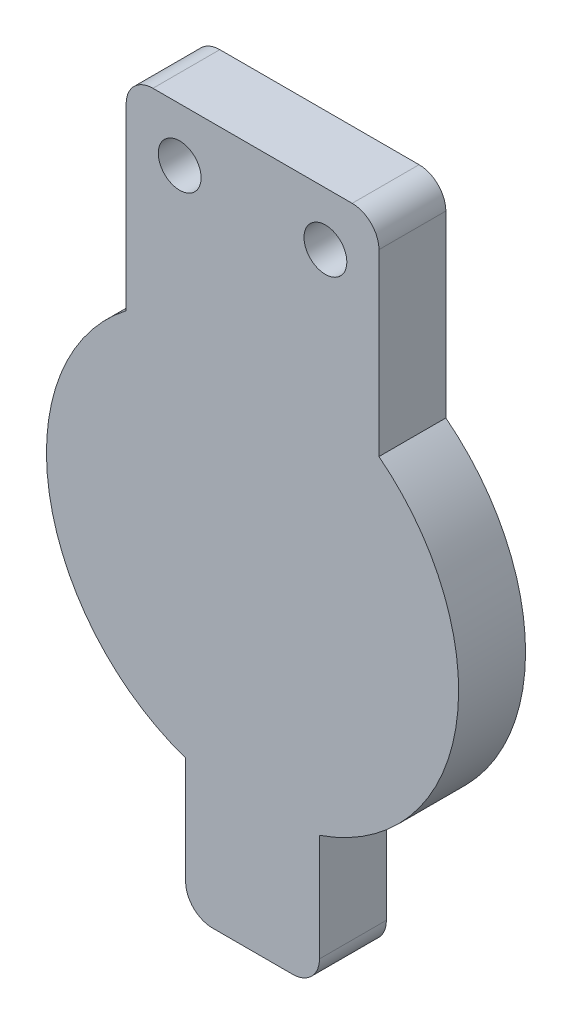
SolidWorks part; units mm, degrees
ref_plane "Front Plane" through (0, 0, 0) normal (0, 0, 1) x (1, 0, 0)
ref_plane "Top Plane" through (0, 0, 0) normal (0, 1, 0) x (1, 0, 0)
ref_plane "Right Plane" through (0, 0, 0) normal (1, 0, 0) x (0, 0, -1)
sketch "Sketch1" plane through (0, 0, 0) normal (0, 0, 1) x (1, 0, 0)
  line L0 (-11.9948, 15.448) -> (-11.9948, 34.9951)
  line L1 (-11.9948, 34.9951) -> (11.9948, 34.9951)
  line L2 (11.9948, 34.9951) -> (11.9948, 15.448)
  line L3 (0, 0) -> (0, 34.9951) construction
  line L4 (-11.9948, 15.448) -> (0, 0) construction
  line L5 (0, 0) -> (11.9948, 15.448) construction
  line L6 (6.9148, 29.9151) -> (0, 36.8298) construction
  line L7 (0, 36.8298) -> (-6.9148, 29.9151) construction
  line L8 (-6.35, -18.4985) -> (-6.35, -31.1985)
  line L9 (-6.35, -31.1985) -> (6.35, -31.1985)
  line L10 (6.35, -31.1985) -> (6.35, -18.4985)
  line L11 (-6.35, -18.4985) -> (6.35, -18.4985)
  arc A0 (-11.9948, 15.448) -> (11.9948, 15.448) centre (0, 0) ccw
  circle A1 centre (6.9148, 29.9151) radius 2.032
  circle A2 centre (-6.9148, 29.9151) radius 2.032
  circle A3 centre (0, 36.8298) radius 12.7 construction
  circle A4 centre (0, 0) radius 19.558 construction
  point P11 (6.9148, 29.9151)
  point P12 (-6.9148, 29.9151)
  point P15 (0, 24.1298)
  point P18 (0, 19.558)
  dimension "D1" = 4.064
  dimension "D2" = 19.558
  dimension "D3" = 9.779
  dimension "D5" = 25.4
  dimension "D7" = 5.08
  dimension "D8" = 5.08
  dimension "D4" = 9.779
  dimension "D6" = 90
  dimension "D9" = 4.5718
  dimension "D10" = 12.7
  dimension "D11" = 12.7
extrude "Boss-Extrude1" add sketch "Sketch1" along normal blind 6.35 contours A0 L8 L9 L10 | L0 A0 L11 L2 L1 A1 A2 | L11 A0
fillet "Fillet1" radius 2.54
